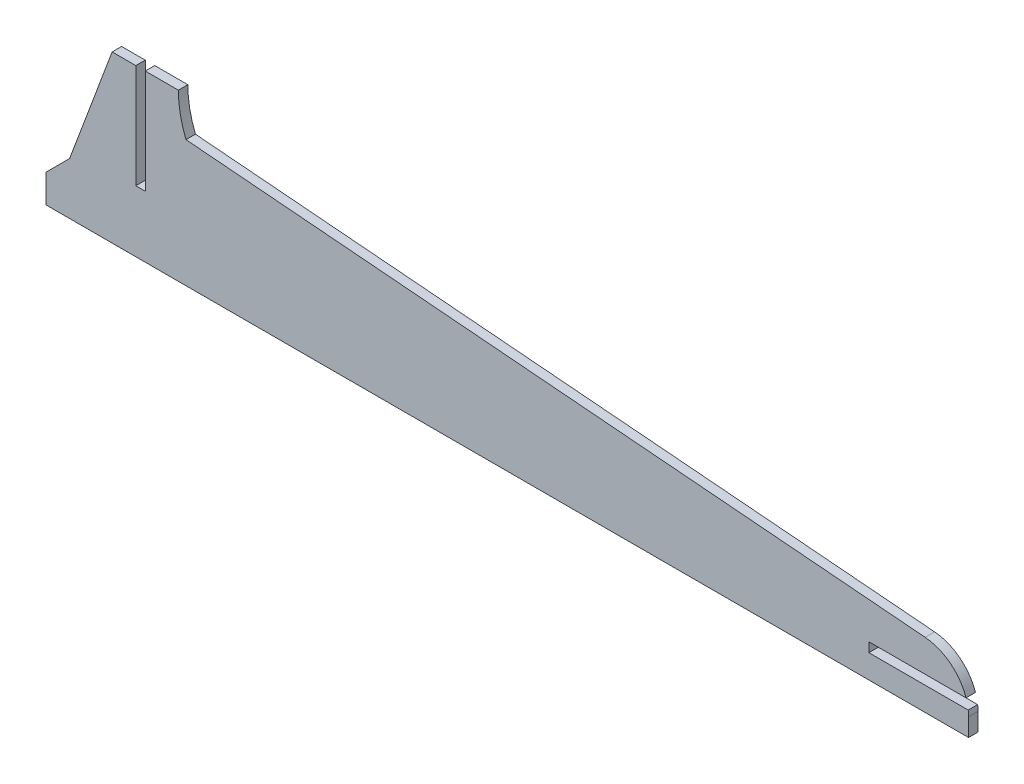
SolidWorks part; units mm, degrees
material "Plástico personalizado"
ref_plane "Plano frontal" through (0, 0, 0) normal (0, 0, 1) x (1, 0, 0)
ref_plane "Plano superior" through (0, 0, 0) normal (0, 1, 0) x (1, 0, 0)
ref_plane "Plano direito" through (0, 0, 0) normal (1, 0, 0) x (0, 0, -1)
sketch "Esboço1" plane through (0, 0, 0) normal (0, 0, 1) x (1, 0, 0)
  line L0 (-99.3896, -14.1808) -> (-99.3896, -8.1808)
  line L1 (-99.3896, -14.1808) -> (95.6104, -14.1808)
  line L3 (-85.4107, 20.8192) -> (-80.4107, 20.8192)
  line L4 (95.6104, -14.1808) -> (95.6104, -10.3843)
  line L5 (-7.7573, 7.4092) -> (-2.3847, 2.2777) construction
  line L6 (74.5377, -7.1808) -> (95.0834, -7.1808)
  line L7 (-99.3896, -8.1808) -> (-94.3896, -3.1808)
  line L8 (-94.3896, -3.1808) -> (-85.4107, 20.8192)
  line L9 (74.5377, -7.1808) -> (74.5377, -9.1808)
  line L10 (-69.8017, 12.5653) -> (86.4386, -0.4186)
  line L11 (-2.3847, 2.2777) -> (13.0161, 5.6829) construction
  line L12 (74.5377, -9.1808) -> (95.5377, -9.1808)
  line L13 (-78.4107, 20.8192) -> (-71.4107, 20.8192)
  line L14 (74.5377, -7.1808) -> (84.5526, -8.2059) construction
  line L15 (74.5377, -9.1808) -> (95.0834, -7.1808) construction
  line L16 (-78.4107, 20.8192) -> (-78.4107, -1.1808)
  line L17 (-78.4107, -1.1808) -> (-80.4107, -1.1808)
  line L18 (-80.4107, 20.8192) -> (-80.4107, -1.1808)
  arc A0 (-71.4107, 20.8192) -> (-69.8017, 12.5653) centre (-49.4352, 20.8192) ccw
  arc A1 (95.6104, -10.3843) -> (95.5377, -9.1808) centre (85.6104, -10.3843) ccw
  arc A2 (95.0834, -7.1808) -> (86.4386, -0.4186) centre (85.6104, -10.3843) ccw
  point P0 (0, 0)
  point P16 (95.6104, -1.1808)
  point P17 (84.5526, -8.2059)
  point P22 (-79.4107, 10.5347)
  dimension "D8" = 10
  dimension "D1" = 195
  dimension "D2" = 35
  dimension "D3" = 6
  dimension "D4" = 24
  dimension "D5" = 13
  dimension "D6" = 14
  dimension "D7" = 5
  dimension "D9" = 21
  dimension "D10" = 5
  dimension "D11" = 5
  dimension "D12" = 2
  dimension "D14" = 2
  dimension "D15" = 22
extrude "Ressalto-extrusão1" add sketch "Esboço1" along normal blind 2
